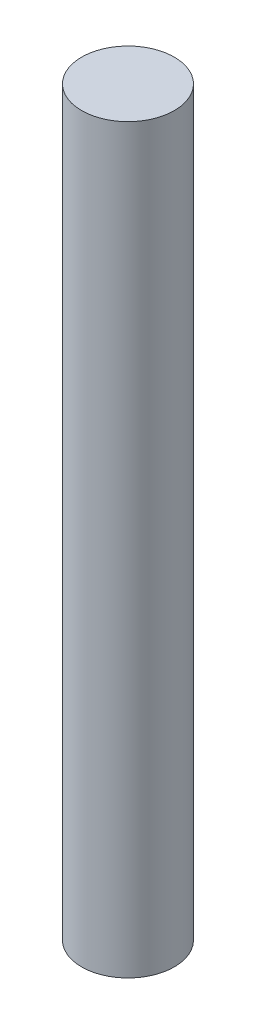
SolidWorks part; units mm, degrees
ref_plane "Alzado" through (0, 0, 0) normal (0, 0, 1) x (1, 0, 0)
ref_plane "Planta" through (0, 0, 0) normal (0, 1, 0) x (1, 0, 0)
ref_plane "Vista lateral" through (0, 0, 0) normal (1, 0, 0) x (0, 0, -1)
sketch "Croquis1" plane through (0, 0, 0) normal (0, 1, 0) x (1, 0, 0)
  circle A0 centre (0, 0) radius 4.7625
  dimension "D1" = 9.525
extrude "Saliente-Extruir1" add sketch "Croquis1" along normal blind 76.2
